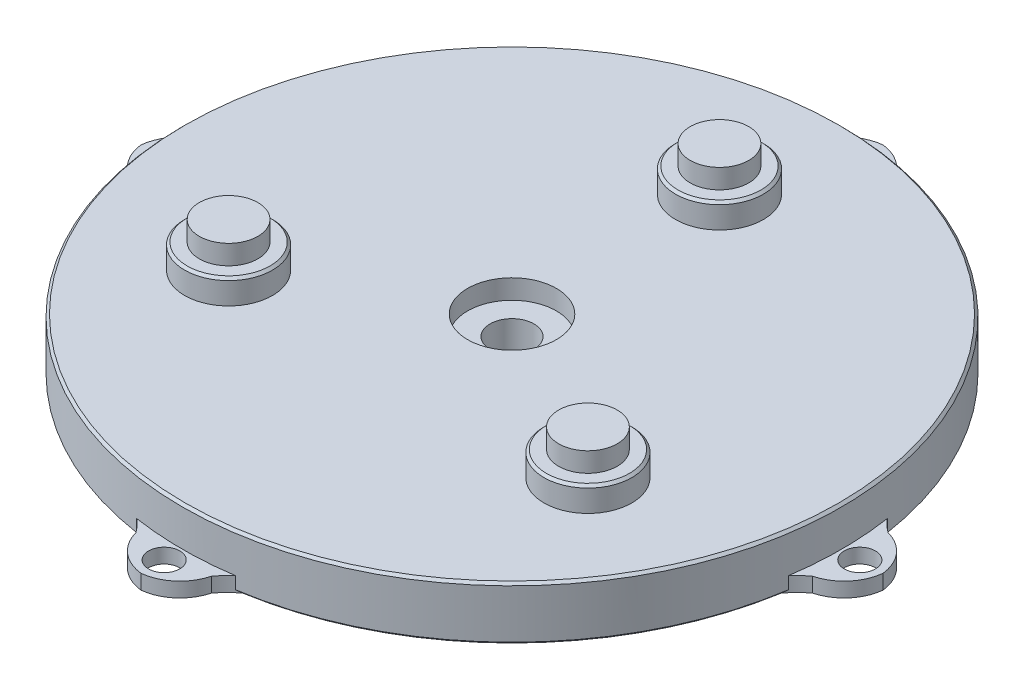
SolidWorks part; units mm, degrees
ref_plane "Front Plane" through (0, 0, 0) normal (0, 0, 1) x (1, 0, 0)
ref_plane "Top Plane" through (0, 0, 0) normal (0, 1, 0) x (1, 0, 0)
ref_plane "Right Plane" through (0, 0, 0) normal (1, 0, 0) x (0, 0, -1)
sketch "Sketch2" plane through (0, 0, 0) normal (0, 1, 0) x (1, 0, 0)
  circle A0 centre (0, 0) radius 65
  dimension "D1" = 130
extrude "Boss-Extrude1" add sketch "Sketch2" along normal blind 11
sketch "Sketch3" plane through (0, 11, 0) normal (0, 1, 0) x (1, 0, 0)
  circle A1 centre (0, 0) radius 9.1
  dimension "D2" = 18.2
extrude "Cut-Extrude2" cut sketch "Sketch3" against normal blind 4
sketch "Sketch4" plane through (0, 7, 0) normal (0, 1, 0) x (1, 0, 0)
  circle A0 centre (0, 0) radius 4.5
  dimension "D1" = 9
extrude "Cut-Extrude4" cut sketch "Sketch4" against normal blind 20
sketch "Sketch5" plane through (0, 0, 0) normal (0, -1, 0) x (1, 0, 0)
  circle A0 centre (0, 0) radius 67.5
  circle A1 centre (0, 0) radius 65
  dimension "D1" = 135
  dimension "D2" = 130
extrude "Boss-Extrude3" add sketch "Sketch5" against normal blind 11
chamfer "Chamfer1" distance 0.5 angle 45 1 edges at (0, 11, -67.5)
chamfer "Chamfer2" distance 0.5 angle 45 1 edges at (0, 0, -67.5)
sketch "Sketch6" plane through (0, 0, 0) normal (0, -1, 0) x (1, 0, 0)
  line L0 (0, 0) -> (0, 77.7457) construction
  line L1 (0, 67) -> (0, 74)
  circle A2 centre (0, 0) radius 67
  circle A4 centre (0, 0) radius 75
  arc A5 (-5.994, 66.7313) -> (0, 74) centre (-0.1299, 68.0014) cw
  arc A6 (5.994, 66.7313) -> (0, 74) centre (0.1299, 68.0014) ccw
  arc A7 (66.7313, -5.994) -> (74, 0) centre (68.0014, -0.1299) ccw
  arc A8 (66.7313, 5.994) -> (74, 0) centre (68.0014, 0.1299) cw
  arc A9 (-5.994, -66.7313) -> (0, -74) centre (-0.1299, -68.0014) ccw
  arc A10 (5.994, -66.7313) -> (0, -74) centre (0.1299, -68.0014) cw
  arc A11 (-66.7313, 5.994) -> (-74, 0) centre (-68.0014, 0.1299) ccw
  arc A12 (-66.7313, -5.994) -> (-74, 0) centre (-68.0014, -0.1299) cw
  arc A13 (-7.9831, 66.5227) -> (-6.0375, 69.0503) centre (-11.5939, 71.3145) ccw
  arc A14 (7.9831, 66.5227) -> (6.0375, 69.0503) centre (11.5939, 71.3145) cw
  arc A15 (66.5227, 7.9831) -> (69.0503, 6.0375) centre (71.3145, 11.5939) ccw
  arc A16 (66.5227, -7.9831) -> (69.0503, -6.0375) centre (71.3145, -11.5939) cw
  arc A17 (7.9831, -66.5227) -> (6.0375, -69.0503) centre (11.5939, -71.3145) ccw
  arc A18 (-7.9831, -66.5227) -> (-6.0375, -69.0503) centre (-11.5939, -71.3145) cw
  arc A19 (-66.5227, -7.9831) -> (-69.0503, -6.0375) centre (-71.3145, -11.5939) ccw
  arc A20 (-66.5227, 7.9831) -> (-69.0503, 6.0375) centre (-71.3145, 11.5939) cw
  point P29 (0, 0)
  point P30 (0, 0)
  point P55 (0, 0)
  circle M6 centre (0, 0) radius 67
  dimension "D1" = 150
  dimension "D2" = 134
  dimension "D4" = 6
  dimension "D8" = 6
  dimension "D3" = 7
  dimension "D5" = 6
  dimension "D7" = 2
  dimension "D6" = 4
  dimension "D9" = 4
extrude "Boss-Extrude8" add sketch "Sketch6" against normal blind 3 contours A5 L1 M6 | A6 L1 M6 | A14 A6 M6 | A13 A2 A5 | A8 A7 M6 | A15 A2 A8 | A16 A7 M6 | A10 A9 M6 | A18 A9 M6 | A17 A2 A10 | A12 A11 M6 | A2 A20 A11 | A19 A2 A12
sketch "Sketch7" plane through (0, 0, 0) normal (0, -1, 0) x (1, 0, 0)
  line L0 (0, 0) -> (0, 118.4865) construction
  line L1 (0, 67) -> (0, 76)
  circle A0 centre (0, 0) radius 82.5
  circle A1 centre (0, 0) radius 67
  arc A2 (-8, 66.5207) -> (0, 76) centre (0.9842, 67.054) cw
  arc A3 (-10.9698, 66.0959) -> (-7.7257, 69.3206) centre (-19.0851, 77.5039) ccw
  arc A4 (8, 66.5207) -> (0, 76) centre (-0.9842, 67.054) ccw
  arc A5 (10.9698, 66.0959) -> (7.7257, 69.3206) centre (19.0851, 77.5039) cw
  arc A6 (66.0959, 10.9698) -> (69.3206, 7.7257) centre (77.5039, 19.0851) ccw
  arc A7 (66.5207, 8) -> (76, 0) centre (67.054, -0.9842) cw
  arc A8 (66.5207, -8) -> (76, 0) centre (67.054, 0.9842) ccw
  arc A9 (66.0959, -10.9698) -> (69.3206, -7.7257) centre (77.5039, -19.0851) cw
  arc A10 (10.9698, -66.0959) -> (7.7257, -69.3206) centre (19.0851, -77.5039) ccw
  arc A11 (8, -66.5207) -> (0, -76) centre (-0.9842, -67.054) cw
  arc A12 (-8, -66.5207) -> (0, -76) centre (0.9842, -67.054) ccw
  arc A13 (-10.9698, -66.0959) -> (-7.7257, -69.3206) centre (-19.0851, -77.5039) cw
  arc A14 (-66.0959, -10.9698) -> (-69.3206, -7.7257) centre (-77.5039, -19.0851) ccw
  arc A15 (-66.5207, -8) -> (-76, 0) centre (-67.054, 0.9842) cw
  arc A16 (-66.5207, 8) -> (-76, 0) centre (-67.054, -0.9842) ccw
  arc A17 (-66.0959, 10.9698) -> (-69.3206, 7.7257) centre (-77.5039, 19.0851) cw
  point P53 (0, 0)
  arc M21 (-7.9831, 66.5227) -> (-66.5227, 7.9831) centre (0, 0) ccw
  arc M22 (-66.5227, 7.9831) -> (-69.0503, 6.0375) centre (-71.3145, 11.5939) cw
  arc M23 (-69.0503, 6.0375) -> (-74, 0) centre (-68.0014, 0.1299) ccw
  arc M24 (-74, 0) -> (-69.0503, -6.0375) centre (-68.0014, -0.1299) ccw
  arc M25 (-69.0503, -6.0375) -> (-66.5227, -7.9831) centre (-71.3145, -11.5939) cw
  arc M26 (-66.5227, -7.9831) -> (-7.9831, -66.5227) centre (0, 0) ccw
  arc M27 (-7.9831, -66.5227) -> (-6.0375, -69.0503) centre (-11.5939, -71.3145) cw
  arc M28 (-6.0375, -69.0503) -> (0, -74) centre (-0.1299, -68.0014) ccw
  arc M29 (0, -74) -> (6.0375, -69.0503) centre (0.1299, -68.0014) ccw
  arc M30 (6.0375, -69.0503) -> (7.9831, -66.5227) centre (11.5939, -71.3145) cw
  arc M31 (7.9831, -66.5227) -> (66.5227, -7.9831) centre (0, 0) ccw
  arc M32 (66.5227, -7.9831) -> (69.0503, -6.0375) centre (71.3145, -11.5939) cw
  arc M33 (69.0503, -6.0375) -> (74, 0) centre (68.0014, -0.1299) ccw
  arc M34 (74, 0) -> (69.0503, 6.0375) centre (68.0014, 0.1299) ccw
  arc M35 (69.0503, 6.0375) -> (66.5227, 7.9831) centre (71.3145, 11.5939) cw
  arc M36 (66.5227, 7.9831) -> (7.9831, 66.5227) centre (0, 0) ccw
  arc M37 (7.9831, 66.5227) -> (6.0375, 69.0503) centre (11.5939, 71.3145) cw
  arc M38 (6.0375, 69.0503) -> (0, 74) centre (0.1299, 68.0014) ccw
  arc M39 (0, 74) -> (-6.0375, 69.0503) centre (-0.1299, 68.0014) ccw
  arc M40 (-6.0375, 69.0503) -> (-7.9831, 66.5227) centre (-11.5939, 71.3145) cw
  dimension "D1" = 165
  dimension "D2" = 134
  dimension "D5" = 9
  dimension "D7" = 14
  dimension "D3" = 9
  dimension "D4" = 8
  dimension "D6" = 3
  dimension "D8" = 4
extrude "Boss-Extrude9" add sketch "Sketch7" against normal blind 3 contours A2 L1 M21 M40 M39 | A1 A4 L1 M38 M37 | A1 A5 A4 | A3 A1 A2 | A1 A16 A15 M26 M25 M24 M23 M22 | A1 A17 A16 | A1 A15 A14 | A1 A13 A12 | A1 A12 A11 M31 M30 M29 M28 M27 | A1 A11 A10 | A1 A9 A8 | A1 A8 A7 M36 M35 M34 M33 M32 | A1 A7 A6
sketch "Sketch8" plane through (0, 0, 0) normal (0, -1, 0) x (1, 0, 0)
  circle A1 centre (0, 71.25) radius 3.2
  circle A2 centre (71.25, 0) radius 3.2
  circle A3 centre (0, -71.25) radius 3.2
  circle A4 centre (-71.25, 0) radius 3.2
  point P14 (0, 0)
  dimension "D2" = 6.4
  dimension "D3" = 4
extrude "Cut-Extrude5" cut sketch "Sketch8" against normal blind 4
sketch "Sketch9" plane through (0, 11, 0) normal (0, 1, 0) x (1, 0, 0)
  line L0 (0, 0) -> (0, 88.7955) construction
  circle A0 centre (0, 0) radius 17.5
  circle A1 centre (0, 0) radius 42.5
  circle A4 centre (0, 42.5) radius 9
  circle A5 centre (0, 0) radius 9.1
  circle A6 centre (36.8061, -21.25) radius 9
  circle A7 centre (-36.8061, -21.25) radius 9
  point P15 (0, 0)
  dimension "D1" = 35
  dimension "D2" = 85
  dimension "D3" = 3
  dimension "D5" = 18
extrude "Boss-Extrude10" add sketch "Sketch9" along normal blind 5 contours L0 A1 A4 | A1 L0 A4 | A4 L0 A1 | L0 A4 A1 | A1 A7 | A1 A7 | A1 A6 | A1 A6
sketch "Sketch10" plane through (0, 16, 0) normal (0, 1, 0) x (1, 0, 0)
  circle A1 centre (0, 42.5) radius 6
  circle A2 centre (36.8061, -21.25) radius 6
  circle A3 centre (-36.8061, -21.25) radius 6
  point P9 (0, 0)
  dimension "D1" = 3
  dimension "D2" = 12
extrude "Boss-Extrude11" add sketch "Sketch10" along normal blind 4
chamfer "Chamfer4" distance 0.5 angle 45 3 edges at (36.8061, 16, 30.25) (-36.8061, 16, 30.25) (0, 16, -33.5)
sketch "Sketch11" plane through (0, 0, 0) normal (0, -1, 0) x (1, 0, 0)
  line L1 (0, 28.5) -> (-28.5, 28.5)
  line L2 (0, 28.5) -> (28.5, 28.5)
  line L3 (-28.5, 28.5) -> (-28.5, -28.5)
  line L4 (-28.5, -28.5) -> (28.5, -28.5)
  line L5 (28.5, -28.5) -> (28.5, 28.5)
  circle A0 centre (-23.5, -23.5) radius 2.5
  circle A1 centre (-23.5, 23.5) radius 2.5
  circle A2 centre (23.5, 23.5) radius 2.5
  circle A3 centre (23.5, -23.5) radius 2.5
  dimension "D8" = 5
  dimension "D9" = 5
  dimension "D10" = 5
  dimension "D11" = 5
  dimension "D2" = 57
  dimension "D3" = 28.5
  dimension "D4" = 57
  dimension "D6" = 47
  dimension "D7" = 47
